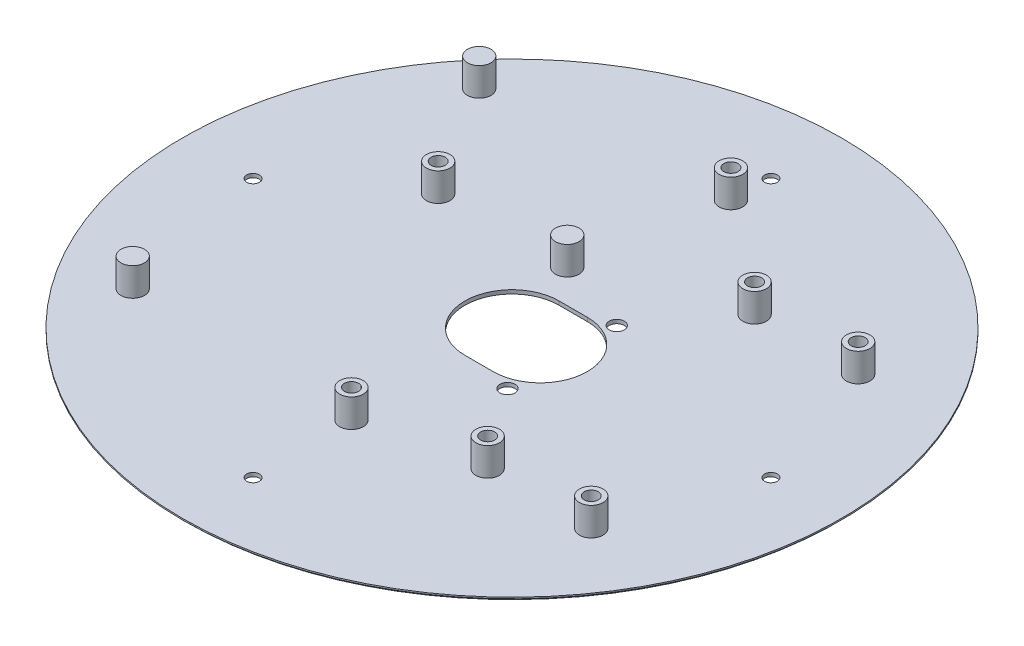
SolidWorks part; units mm, degrees
ref_plane "Ebene vorne" through (0, 0, 0) normal (0, 0, 1) x (1, 0, 0)
ref_plane "Ebene oben" through (0, 0, 0) normal (0, 1, 0) x (1, 0, 0)
ref_plane "Ebene rechts" through (0, 0, 0) normal (1, 0, 0) x (0, 0, -1)
sketch "Skizze1" plane through (0, 0, 0) normal (0, 1, 0) x (1, 0, 0)
  circle A0 centre (0, 0) radius 70
  dimension "D1" = 140
extrude "Aufsatz-Linear austragen1" add sketch "Skizze1" along normal blind 0.8
sketch "Skizze3" plane through (0, 0, 0) normal (0, -1, 0) x (1, 0, 0)
  line L0 (6, 0) -> (0, 0) construction
  line L1 (6, -10) -> (0, -10)
  line L2 (6, 10) -> (0, 10)
  arc A0 (6, -10) -> (6, 10) centre (6, 0) ccw
  arc A1 (0, 10) -> (0, -10) centre (0, 0) ccw
  point P2 (3, 0)
  point P4 (19.3628, 0)
  dimension "D1" = 20
  dimension "D2" = 6
extrude "Schnitt-Linear austragen1" cut sketch "Skizze3" against normal up to next
sketch "Skizze2" plane through (0, 0.8, 0) normal (0, 1, 0) x (1, 0, 0)
  circle A0 centre (-32.5332, 16.8549) radius 1.5
  circle A1 centre (-0.2807, 46.78) radius 1.5
  circle A2 centre (23.2607, 28.2715) radius 1.5
  circle A3 centre (45.2607, 28.2715) radius 1.5
  circle A4 centre (45.2607, -28.4285) radius 1.5
  circle A5 centre (23.2607, -28.4285) radius 1.5
  circle A6 centre (-0.153, -33.9402) radius 1.5
  circle A7 centre (-47.534, 40.5718) radius 2.5
  circle A8 centre (-5.2934, 17.0303) radius 2.5
  circle A9 centre (-47.534, -33.0275) radius 2.5
  circle A10 centre (-32.5332, 16.8549) radius 2.5
  circle A11 centre (-0.2807, 46.78) radius 2.5
  circle A12 centre (23.2607, 28.2715) radius 2.5
  circle A13 centre (45.2607, 28.2715) radius 2.5
  circle A14 centre (45.2607, -28.4285) radius 2.5
  circle A15 centre (23.2607, -28.4285) radius 2.5
  circle A16 centre (-0.153, -33.9402) radius 2.5
  dimension "D1" = 3
  dimension "D2" = 5
  dimension "D3" = 1
extrude "Aufsatz-Linear austragen2" add sketch "Skizze2" along normal blind 6 and the other way up to surface (0.8 mm away) other way up to face at (3, 0, 0)
sketch "Skizze4" plane through (0, 0.8, 0) normal (0, 1, 0) x (1, 0, 0)
  circle A0 centre (-32.5332, 16.8549) radius 1.5 construction
  circle A1 centre (23.2607, 28.2715) radius 1.5 construction
  circle A2 centre (45.2607, 28.2715) radius 1.5 construction
  circle A3 centre (45.2607, -28.4285) radius 1.5 construction
  circle A4 centre (23.2607, -28.4285) radius 1.5 construction
  circle A5 centre (-0.153, -33.9402) radius 1.5 construction
  circle A6 centre (-0.2807, 46.78) radius 1.4101 construction
  circle A7 centre (-32.5332, 16.8549) radius 1.5
  circle A8 centre (23.2607, 28.2715) radius 1.5
  circle A9 centre (45.2607, 28.2715) radius 1.5
  circle A10 centre (45.2607, -28.4285) radius 1.5
  circle A11 centre (23.2607, -28.4285) radius 1.5
  circle A12 centre (-0.153, -33.9402) radius 1.5
  circle A13 centre (-0.2807, 46.78) radius 1.4101
extrude "Schnitt-Linear austragen2" cut sketch "Skizze4" against normal through all
chamfer "Fase1" distance 0.5 angle 45 1 edges at (0, 0, 70)
sketch "Skizze5" plane through (0, 0, 0) normal (0, -1, 0) x (1, 0, 0)
  line L0 (69.5, 0) -> (-69.5, 0) construction
  circle A0 centre (0, 0) radius 69.5 construction
  circle A1 centre (0, 0) radius 55 construction
  circle A2 centre (-55, 0) radius 1.35
  circle A3 centre (55, 0) radius 1.35
  circle A4 centre (0, -55) radius 1.35
  circle A5 centre (0, 55) radius 1.35
  dimension "D1" = 2.7
  dimension "D2" = 110
extrude "Schnitt-Linear austragen3" cut sketch "Skizze5" against normal up to next
sketch "Skizze6" plane through (0, 0, 0) normal (0, -1, 0) x (-1, 0, 0)
  circle A0 centre (-10.6442, 11.6052) radius 1.6
  circle A1 centre (-10.6442, -11.6052) radius 1.6
  dimension "D1" = 3.2
extrude "Schnitt-Linear austragen4" cut sketch "Skizze6" against normal blind 4
